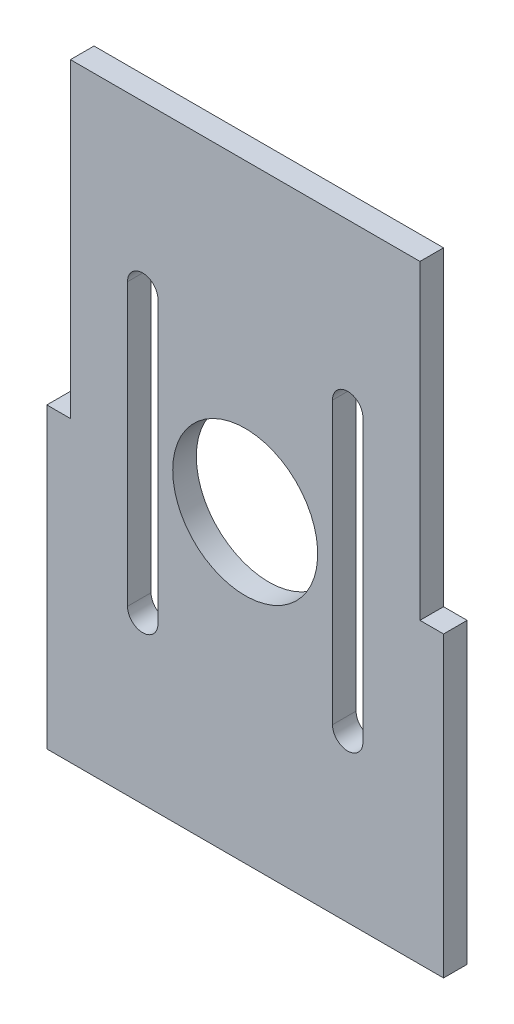
SolidWorks part; units mm, degrees
material "Teak"
ref_plane "Front Plane" through (0, 0, 0) normal (0, 0, 1) x (1, 0, 0)
ref_plane "Top Plane" through (0, 0, 0) normal (0, 1, 0) x (1, 0, 0)
ref_plane "Right Plane" through (0, 0, 0) normal (1, 0, 0) x (0, 0, -1)
sketch "Sketch3" plane through (0, 0, 0) normal (0, 0, 1) x (1, 0, 0)
  line L0 (0, -10.35) -> (0, 0) construction
  line L1 (-22.965, -40) -> (22.965, -40)
  line L2 (-22.965, -40) -> (-22.965, 40)
  line L3 (-22.965, 40) -> (22.965, 40)
  line L4 (22.965, -40) -> (22.965, 40)
  line L5 (-22.965, -40) -> (22.965, 40) construction
  line L6 (-22.965, 40) -> (22.965, -40) construction
  line L7 (-12.5, -30.7) -> (12.5, -30.7)
  line L8 (-12.5, -30.7) -> (-12.5, 10)
  line L9 (-12.5, 10) -> (12.5, 10)
  line L10 (12.5, -30.7) -> (12.5, 10)
  line L11 (-12.5, -30.7) -> (12.5, 10) construction
  line L12 (-12.5, 10) -> (12.5, -30.7) construction
  line L13 (0, -10.35) -> (-12.5, -10.35) construction
  line L14 (-12.5, -34.85) -> (12.5, -34.85) construction
  line L15 (-12.5, 14.15) -> (12.5, 14.15) construction
  line L16 (-12.5, 11.65) -> (12.5, 11.65)
  line L17 (-12.5, 16.65) -> (12.5, 16.65)
  line L18 (-12.5, -34.85) -> (12.5, -34.85) construction
  line L19 (-12.5, -32.35) -> (12.5, -32.35)
  line L20 (-12.5, -37.35) -> (12.5, -37.35)
  circle A0 centre (0, 0) radius 3.3834 construction
  arc A1 (-12.5, 11.65) -> (-12.5, 16.65) centre (-12.5, 14.15) cw
  arc A2 (12.5, 16.65) -> (12.5, 11.65) centre (12.5, 14.15) cw
  arc A3 (-12.5, -32.35) -> (-12.5, -37.35) centre (-12.5, -34.85) ccw
  arc A4 (12.5, -37.35) -> (12.5, -32.35) centre (12.5, -34.85) ccw
  point P0 (0, -10.35)
  point P15 (0, 0)
  dimension "D1" = 40.7
  dimension "D5" = 10
  dimension "D6" = 49
  dimension "D2" = 45.93
  dimension "D3" = 80
  dimension "D4" = 25
  dimension "D7" = 5
extrude "Boss-Extrude3" [suppressed] add sketch "Sketch3" along normal blind 3.1
sketch "Sketch4" [suppressed] plane through (0, 0, 0) normal (0, 0, 1) x (1, 0, 0)
  line L0 (22.965, 0) -> (22.965, -40)
  line L1 (22.965, 0) -> (26.065, 0)
  line L2 (22.965, -40) -> (26.065, -40)
  line L3 (26.065, 0) -> (26.065, -40)
  line L5 (0, 0) -> (0, -32.5) construction
  line L7 (-26.065, 0) -> (-26.065, -40)
  line L8 (-22.965, -40) -> (-26.065, -40)
  line L9 (-22.965, 0) -> (-26.065, 0)
  line L10 (-22.965, 0) -> (-22.965, -40)
  line L11 (22.965, -40) -> (22.965, 40) construction
  dimension "D1" = 3.1
extrude "Boss-Extrude4" [suppressed] add sketch "Sketch4" along normal through all
sketch "Sketch5" plane through (0, 0, 0) normal (0, 0, 1) x (1, 0, 0)
  line L1 (-22.965, -40) -> (22.965, -40)
  line L2 (-22.965, -40) -> (-22.965, 40)
  line L3 (-22.965, 40) -> (22.965, 40)
  line L4 (22.965, -40) -> (22.965, 40)
  line L5 (-22.965, -40) -> (22.965, 40) construction
  line L6 (-22.965, 40) -> (22.965, -40) construction
  point P0 (0, 0)
  dimension "D2" = 45.93
  dimension "D3" = 80
extrude "Boss-Extrude5" add sketch "Sketch5" along normal blind 3.1
sketch "Sketch6" plane through (0, 0, 0) normal (0, 0, 1) x (1, 0, 0)
  line L0 (22.965, -0.8462) -> (22.965, -40)
  line L1 (22.965, -0.8462) -> (26.065, -0.8462)
  line L2 (22.965, -40) -> (26.065, -40)
  line L3 (26.065, -0.8462) -> (26.065, -40)
  line L4 (22.965, -40) -> (22.965, 40) construction
  line L5 (0, 0) -> (0, -32.5) construction
  line L6 (-22.965, -40) -> (22.965, -40) construction
  line L7 (-26.065, -0.8462) -> (-26.065, -40)
  line L8 (-22.965, -40) -> (-26.065, -40)
  line L9 (-22.965, -0.8462) -> (-26.065, -0.8462)
  line L10 (-22.965, -0.8462) -> (-22.965, -40)
  dimension "D1" = 3.1
  dimension "D2" = 0
  dimension "D3" = 0
extrude "Boss-Extrude6" add sketch "Sketch6" along normal through all
sketch "Sketch7" plane through (0, 0, 0) normal (0, 0, 1) x (1, 0, 0)
  line L0 (-40, 40) -> (40, -40) construction
  line L1 (40, 40) -> (-40, -40) construction
  line L2 (-13.4704, 13.4704) -> (-13.4704, -13.4704) construction
  line L3 (-13.4704, 13.4704) -> (-11.4704, 13.4704) construction
  line L4 (0, 0) -> (57.4877, 0) construction
  line L5 (-11.4704, -13.4704) -> (-13.4704, -13.4704) construction
  line L6 (-15.4704, 13.4704) -> (-15.4704, -13.4704)
  line L7 (0, -40) -> (0, 40) construction
  line L8 (-15.4704, 13.4704) -> (-15.4704, 18.4704)
  line L9 (-15.4704, -13.4704) -> (-15.4704, -18.4704)
  line L10 (-11.4704, -13.4704) -> (-11.4704, -18.4704)
  line L11 (-11.4704, 13.4704) -> (-11.4704, -13.4704)
  line L12 (-11.4704, 13.4704) -> (-11.4704, 18.4704)
  line L13 (11.4704, -13.4704) -> (13.4704, -13.4704) construction
  line L14 (13.4704, 13.4704) -> (11.4704, 13.4704) construction
  line L19 (13.4704, 13.4704) -> (13.4704, -13.4704) construction
  line L20 (11.4704, 13.4704) -> (11.4704, 18.4704)
  line L21 (11.4704, 13.4704) -> (11.4704, -13.4704)
  line L22 (11.4704, -13.4704) -> (11.4704, -18.4704)
  line L23 (15.4704, -13.4704) -> (15.4704, -18.4704)
  line L24 (15.4704, 13.4704) -> (15.4704, 18.4704)
  line L25 (15.4704, 13.4704) -> (15.4704, -13.4704)
  arc A0 (-11.4704, 18.4704) -> (-15.4704, 18.4704) centre (-13.4704, 18.4704) ccw
  arc A1 (-15.4704, -18.4704) -> (-11.4704, -18.4704) centre (-13.4704, -18.4704) ccw
  arc A2 (15.4704, -18.4704) -> (11.4704, -18.4704) centre (13.4704, -18.4704) cw
  arc A3 (11.4704, 18.4704) -> (15.4704, 18.4704) centre (13.4704, 18.4704) cw
  circle A4 centre (0, 0) radius 9.525
  point P11 (0, 0)
  dimension "D1" = 26.9408
  dimension "D5" = 19.05
  dimension "D2" = 5
  dimension "D6" = 2
  dimension "D3" = 0
  dimension "D7" = 80
  dimension "D8" = 80
extrude "Cut-Extrude2" cut sketch "Sketch7" along normal through all
equation "\"thick\" = 3.1mm"
equation "\"small_bearing_outer\"=12.9mm"
equation "\"servo1_L\"=40.7mm"
equation "\"servo1_W\"=20.5mm"
equation "\"servo1_H\"=43.5mm"
equation "\"servo1_hL\"=49mm"
equation "\"servo1_hW\"=10mm"
equation "\"servo1_H2\"=27mm"
equation "\"large_bearing_inner\"=2.75in"
equation "\"large_bearing_outer\"=4.75in"
equation "\"large_bearing_thick\"=3/8in"
equation "\"large_bearing_h1\"=3.25in"
equation "\"large_bearing_h2\"=4.25in"
equation "\"D1@Sketch3\"=\"servo1_L\""
equation "\"D6@Sketch3\"=\"servo1_hL\""
equation "\"D1@Boss-Extrude5\"=\"thick\""
equation "\"D2@Sketch3\"=33.53 + 4*\"thick\""
equation "\"D2@Sketch5\"=33.53+4*\"thick\""
